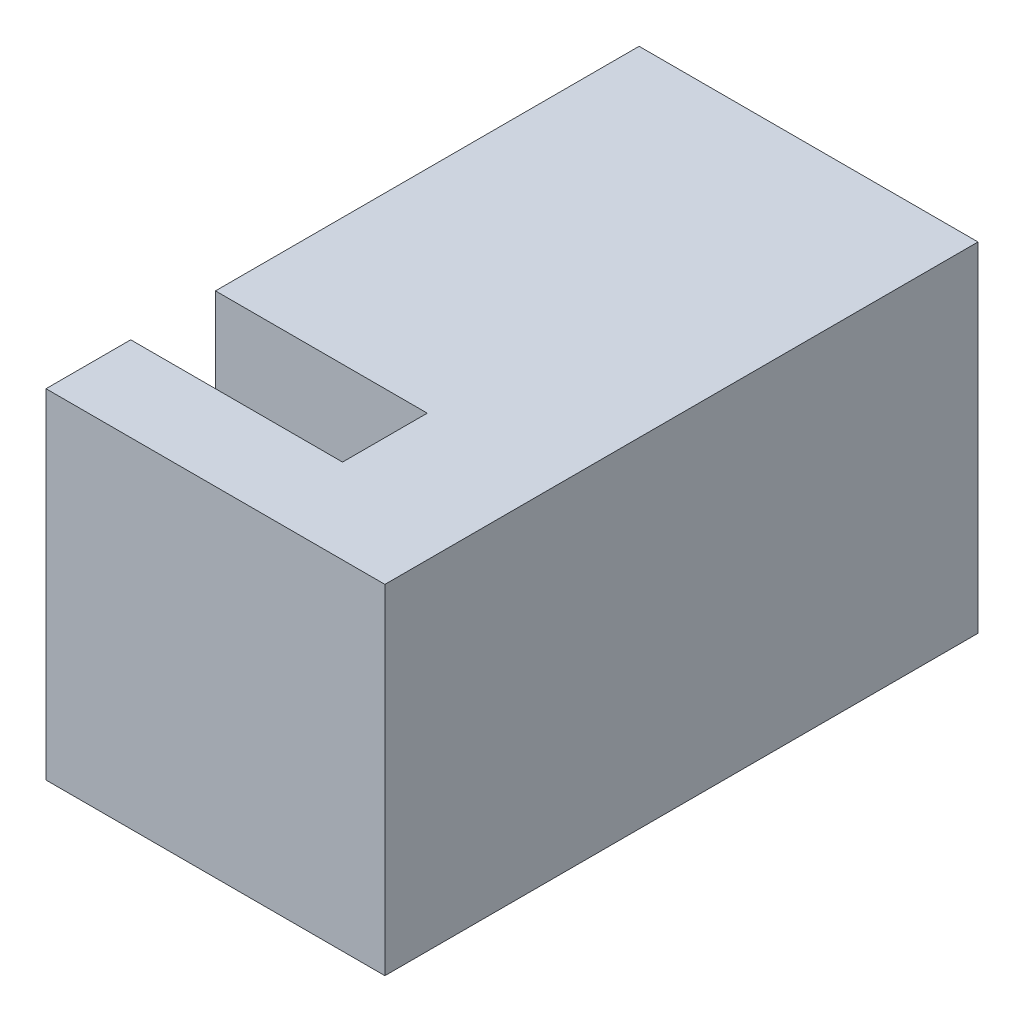
SolidWorks part; units mm, degrees
ref_plane "Płaszczyzna przednia" through (0, 0, 0) normal (0, 0, 1) x (1, 0, 0)
ref_plane "Płaszczyzna górna" through (0, 0, 0) normal (0, 1, 0) x (1, 0, 0)
ref_plane "Płaszczyzna prawa" through (0, 0, 0) normal (1, 0, 0) x (0, 0, -1)
sketch "Szkic1" plane through (0, 0, 0) normal (0, 0, 1) x (1, 0, 0)
  line L1 (0, 0) -> (8, 0)
  line L2 (0, 0) -> (0, 8)
  line L3 (0, 8) -> (8, 8)
  line L4 (8, 0) -> (8, 8)
  dimension "D1" = 8
  dimension "D2" = 8
extrude "Dodanie-wyciągnięcie1" add sketch "Szkic1" along normal blind 14
sketch "Szkic2" plane through (0, 8, 0) normal (0, 1, 0) x (1, 0, 0)
  line L0 (0, -14) -> (0, 0) construction
  line L1 (0, -10) -> (5, -10)
  line L2 (0, -10) -> (0, -12)
  line L3 (0, -12) -> (5, -12)
  line L6 (8, 0) -> (0, 0) construction
  line L7 (5, -10) -> (5, -12)
  dimension "D1" = 10
  dimension "D2" = 2
  dimension "D3" = 5
extrude "Wytnij-wyciągnięcie1" cut sketch "Szkic2" against normal blind 5
sketch "Szkic3" plane through (0, 0, 0) normal (0, 0, -1) x (-1, 0, 0)
  line L0 (0, 0) -> (-8, 0) construction
  line L1 (-8, 0) -> (-8, 8) construction
  circle A0 centre (-4, 4) radius 1.375
  dimension "D3" = 2.75
  dimension "D1" = 4
  dimension "D2" = 4
extrude "Wytnij-wyciągnięcie2" cut sketch "Szkic3" against normal blind 9
